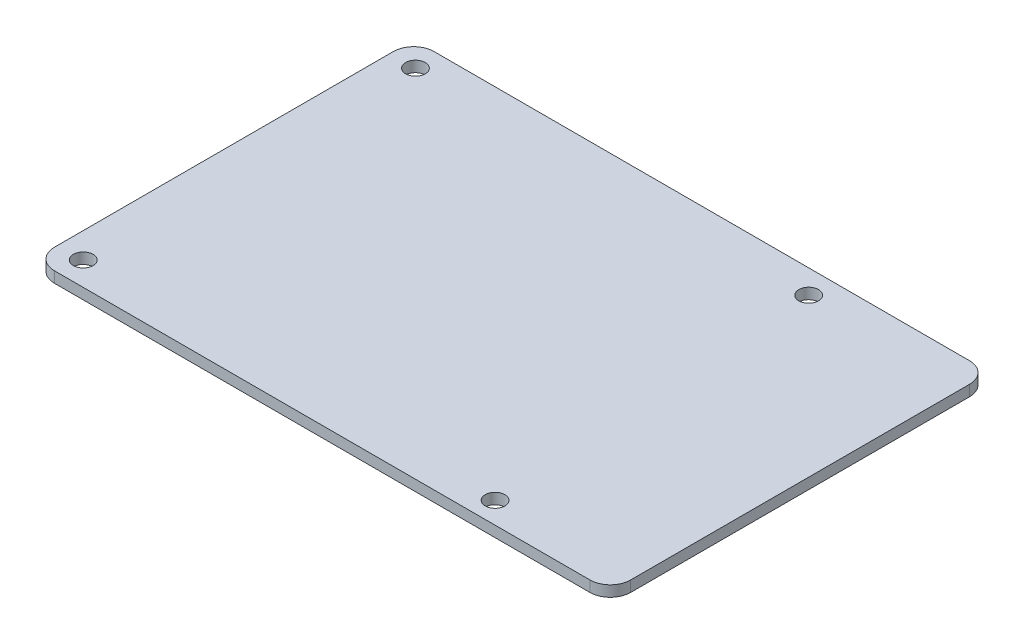
SolidWorks part; units mm, degrees
ref_plane "Front" through (0, 0, 0) normal (0, 0, 1) x (1, 0, 0)
ref_plane "Top" through (0, 0, 0) normal (0, 1, 0) x (1, 0, 0)
ref_plane "Right" through (0, 0, 0) normal (1, 0, 0) x (0, 0, -1)
sketch "Sketch1" plane through (0, 0, 0) normal (0, 1, 0) x (1, 0, 0)
  line L1 (-39.5, 28) -> (39.5, 28)
  line L2 (-42.5, 25) -> (-42.5, -25)
  line L3 (-39.5, -28) -> (39.5, -28)
  line L4 (42.5, 25) -> (42.5, -25)
  line L5 (-42.5, 28) -> (42.5, -28) construction
  line L6 (-42.5, -28) -> (42.5, 28) construction
  arc A0 (-42.5, -25) -> (-39.5, -28) centre (-39.5, -25) ccw
  arc A1 (39.5, -28) -> (42.5, -25) centre (39.5, -25) ccw
  arc A2 (39.5, 28) -> (42.5, 25) centre (39.5, 25) cw
  arc A3 (-39.5, 28) -> (-42.5, 25) centre (-39.5, 25) ccw
  point P0 (0, 0)
  dimension "D3" = 3
  dimension "D1" = 85
  dimension "D2" = 56
extrude "Boss-Extrude1" add sketch "Sketch1" along normal blind 1.6
hole_wizard "M2.5 Clearance Hole1" positions "Sketch3" profile "Sketch2" hole size "M2.5" standard "ANSI Metric" end condition through all
sketch "Sketch3" plane through (0, 1.6, 0) normal (0, 1, 0) x (1, 0, 0)
  line L0 (-39.5, -28) -> (39.5, -28) construction
  point P0 (-38.7428, 24.5)
  point P2 (19.2572, 24.5)
  point P4 (22.3269, -24.8249)
  point P6 (-38.7428, -24.5)
  dimension "D1" = 58
  dimension "D2" = 49
  dimension "D3" = 3.5
sketch "Sketch2" plane through (-38.7428, 1.6, -24.5) normal (1, 0, 0) x (0, 0, 1)
  line L0 (0, 0) -> (0, 1.6)
  line L1 (0, 1.6) -> (1.45, 1.6)
  line L2 (1.45, 1.6) -> (1.45, 0)
  line L5 (1.45, 0) -> (0, 0)
  line L11 (0, -6.35) -> (0, 107.95) construction
  dimension "Thru Hole Dia." = 2.9
  dimension "Thru Hole Depth" = 1.6
